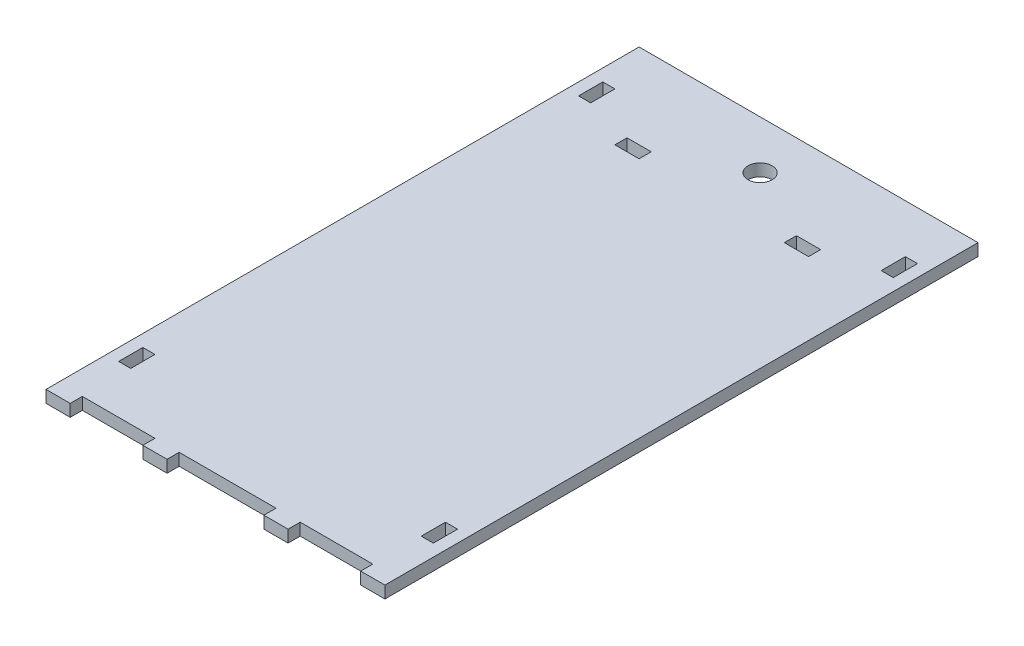
SolidWorks part; units mm, degrees
material "Beech"
ref_plane "Front Plane" through (0, 0, 0) normal (0, 0, 1) x (1, 0, 0)
ref_plane "Top Plane" through (0, 0, 0) normal (0, 1, 0) x (1, 0, 0)
ref_plane "Right Plane" through (0, 0, 0) normal (1, 0, 0) x (0, 0, -1)
sketch "Sketch1" plane through (0, 0, 0) normal (0, 1, 0) x (1, 0, 0)
  line L0 (0, 0) -> (177.8, 0)
  line L1 (0, 0) -> (0, 304.8)
  line L2 (177.8, 0) -> (177.8, 304.8)
  line L3 (0, 304.8) -> (177.8, 304.8)
  line L4 (0, 0) -> (12.7, 0)
  line L5 (0, 0) -> (0, -6.35)
  line L6 (12.7, 0) -> (12.7, -6.35)
  line L7 (0, -6.35) -> (12.7, -6.35)
  line L8 (177.8, 0) -> (165.1, 0)
  line L9 (177.8, 0) -> (177.8, -6.35)
  line L10 (165.1, 0) -> (165.1, -6.35)
  line L11 (177.8, -6.35) -> (165.1, -6.35)
  line L12 (127, 0) -> (114.3, 0)
  line L13 (127, 0) -> (127, -6.35)
  line L14 (114.3, 0) -> (114.3, -6.35)
  line L15 (127, -6.35) -> (114.3, -6.35)
  line L16 (50.8, 0) -> (63.5, 0)
  line L17 (50.8, 0) -> (50.8, -6.35)
  line L18 (63.5, 0) -> (63.5, -6.35)
  line L19 (50.8, -6.35) -> (63.5, -6.35)
  line L20 (165.1, 279.4) -> (171.45, 279.4)
  line L21 (165.1, 279.4) -> (165.1, 266.7)
  line L22 (171.45, 279.4) -> (171.45, 266.7)
  line L23 (165.1, 266.7) -> (171.45, 266.7)
  line L24 (6.35, 279.4) -> (12.7, 279.4)
  line L25 (6.35, 279.4) -> (6.35, 266.7)
  line L26 (12.7, 279.4) -> (12.7, 266.7)
  line L27 (6.35, 266.7) -> (12.7, 266.7)
  line L28 (6.35, 38.1) -> (12.7, 38.1)
  line L29 (6.35, 38.1) -> (6.35, 25.4)
  line L30 (12.7, 38.1) -> (12.7, 25.4)
  line L31 (6.35, 25.4) -> (12.7, 25.4)
  line L32 (165.1, 38.1) -> (171.45, 38.1)
  line L33 (165.1, 38.1) -> (165.1, 25.4)
  line L34 (171.45, 38.1) -> (171.45, 25.4)
  line L35 (165.1, 25.4) -> (171.45, 25.4)
  line L36 (38.1, 260.35) -> (38.1, 254)
  line L37 (38.1, 260.35) -> (50.8, 260.35)
  line L38 (38.1, 254) -> (50.8, 254)
  line L39 (50.8, 260.35) -> (50.8, 254)
  line L40 (127, 260.35) -> (127, 254)
  line L41 (127, 260.35) -> (139.7, 260.35)
  line L42 (127, 254) -> (139.7, 254)
  line L43 (139.7, 260.35) -> (139.7, 254)
  circle A0 centre (88.9, 279.4) radius 6.35
  point P21 (88.9, 304.8)
  dimension "D8" = 12.7
  dimension "D1" = 177.8
  dimension "D2" = 6.35
  dimension "D3" = 12.7
  dimension "D4" = 50.8
  dimension "D5" = 50.8
  dimension "D6" = 304.8
  dimension "D7" = 25.4
  dimension "D9" = 25.4
  dimension "D10" = 25.4
  dimension "D11" = 254
  dimension "D12" = 38.1
  dimension "D13" = 38.1
extrude "Boss-Extrude1" add sketch "Sketch1" along normal blind 6.35 contours L3 L1 L0 L2 A0 L37 L39 L38 L36 L35 L33 L32 L34 L31 L29 L28 L30 L27 L25 L24 L26 L23 L21 L20 L22 L41 L43 L42 L40 | L5 L7 L6 L0 | L17 L19 L18 L0 | L15 L13 L0 L14 | L11 L9 L0 L10
equation "\"CageLeftBottomEdge\"=22.11mm"
equation "\"CageLeftTopEdge\"=22.11mm"
equation "\"CageRightBottomEdge\"=21.63mm"
equation "\"CageRightTopEdge\"=21.63mm"
equation "\"CageHeight\"=86.04mm"
equation "\"CageLength\"=73.76mm"
equation "\"CageTopScrewClearance\"=10mm"
equation "\"CageBottomScrewClearance\"=25mm"
equation "\"CageLeftTopDepth\"= 11.65mm"
equation "\"CageLeftBottomDepth\"=11.11mm"
equation "\"CageLeftTopHeight\"=8.56175mm"
equation "\"CageLeftBottomHeight\"=16mm"
equation "\"CageRightTopDepth\"= 11.05mm"
equation "\"CageRightBottomDepth\"=10.58mm"
equation "\"CageRightTopHeight\"=9.6mm"
equation "\"CageRightBottomHeight\"=15.49mm"
equation "\"CageLeftTopChannelDepth\"=2.41908mm"
equation "\"CageLeftBottomChannelDepth\"=2.588mm"
equation "\"CageLeftChannelHeight\"=11.7mm"
equation "\"CageRightTopChannelDepth\"=2.32mm"
equation "\"CageRightBottomChannelDepth\"=2.318mm"
equation "\"CageRightChannelHeight\"=10mm"
equation "\"CageChanRelHeight\"=23.99mm"
equation "\"CageChanRelDepth\"=5.492mm"
equation "\"CageChamberRadius\"=16.261mm"
equation "\"CageScrewDiameter\"=4.8mm"
equation "\"CageSetScrewDiameter\"=3.5mm"
equation "\"CageAxleRadius\"=6.639mm"
equation "\"CageAxleKeyHeight\"=1.619mm"
equation "\"CageAxleKeyWidth\"=2.662mm"
equation "\"CageHoseWindowWidth\"=16.29mm"
equation "\"CageHoseWindowHeight\"=26.5mm"
equation "\"CageHoseWindow-Edge\"=8.89mm"
equation "\"CageScrew-VerticalEdge\"=5.0mm"
equation "\"CageScrew-HorizontalEdge\"=7.5mm"
equation "\"CageScrew-HoseCornerScrewEdge\"=4.45mm"
equation "\"CageAxle-BottomEdge\"=56.05mm"
equation "\"CageAxle-FrontEdge\"=46.03mm"
equation "\"CageBackSetScrew-Axle\"=40mm"
equation "\"CageFrontSetScrew-Axle\"=22mm"
equation "\"CageVelocityWindow-BackEdge\"=34.8mm"
equation "\"CageVelocityWindow-BottomEdge\"=27.55mm"
equation "\"CageVelocityWindowHeight\"=22.29mm"
equation "\"CageVelocityWindowWidth\"=12.61mm"
equation "\"TriggerSlot-BottomEdge\"=6.35mm"
equation "\"TriggerSlot-FrontEdge\"=15mm"
equation "\"TriggerSlotSize\"=6.7mm"
equation "\"TriggerRackOffset\"=.236224in"
equation "\"TriggerSlotSizeInt\"=.25in"
equation "\"MotorMountLegLength\"=.25in"
equation "\"GearOffset\"=.264907in"
equation "\"TriggerSlotSpacing\"=.25in"
equation "\"TriggerMiniSlotWidth\"=3.5mm"
equation "\"TriggerRackWidth\"=6.5mm"
equation "\"TGMGearFaceDiameter\"=24.40mm"
equation "\"TGMCylinderLength\"=15.00mm"
equation "\"TGMScrewHole-Center\"=8.70mm"
equation "\"TGMScrewHoleDiameter\"=5.04mm"
equation "\"TGMCenterHoleDiameter\"=9.50mm"
equation "\"TGMShaftCollarSideLength\"=19.00mm"
equation "\"TGMShaftCollarDockingDepth\"=7.00mm"
equation "\"whitemotordepth\"=11.27mm"
equation "\"whitemotorbackdepth\"=3.845mm"
equation "\"whitemotoraxledepth\" = 3.5mm"
equation "\"whitemotoraxleoffset\"=11.4mm"
equation "\"whitemotorwidth\"=12.07mm"
equation "\"whitemotorheight\"=16.68mm"
equation "\"whitemotorcylinderlength\" =13.04mm"
equation "\"whitemotorcylinderradius\"=3.845mm"
equation "\"whitemotorcylinderoffset\"=2.35mm"
equation "\"whitemotorcutoutlength\"=1.88mm"
equation "\"whitemotorouterrad\"=5mm"
equation "\"whitemotorinnerrad\"=2.95mm"
equation "\"elasticracklength\"=2in"
equation "\"elasticrackpegsize\"=.25in"
equation "\"elasticrackpegbuffer\"=.125in"
equation "\"elasticrackpegspacing\"=1.76476378in"
equation "\"elasticbaybuffer\"=.25in"
equation "\"elasticdepth\"=.125in"
equation "\"elasticbaydepth\"=.75in"
equation "\"motormountwidth\"=12mm"
equation "\"motormountcornerfillet\"=3mm"
equation "\"pandiscradius\"=14in"
equation "\"towermaterialwidth\"=.25in"
equation "\"towerslotlength\"=.5in"
equation "\"towermarkerspace\"=5in"
equation "\"towerslothorizoffset\"=1in"
equation "\"towerslothorizspacing\"=2in"
equation "\"towerslotvertoffset\"=3in"
equation "\"towerslotvertspacing\"=1in"
equation "\"towerheight\"=12in"
equation "\"towerupslot\"=1in"
equation "\"D1@Sketch1\"=(\"towerslothorizoffset\"+\"towerslothorizspacing\"+\"towerslotlength\")*2"
equation "\"D2@Sketch1\"=\"towermaterialwidth\""
equation "\"D3@Sketch1\"=\"towerslotlength\""
equation "\"D4@Sketch1\"=\"towerslothorizspacing\""
equation "\"D5@Sketch1\"=\"towerslothorizspacing\""
equation "\"D6@Sketch1\"=\"towerheight\""
equation "\"D7@Sketch1\"=\"towerupslot\""
equation "\"toweraxle\"=.5in"
equation "\"D8@Sketch1\"=\"toweraxle\""
equation "\"D9@Sketch1\"=\"towerupslot\""
equation "\"D10@Sketch1\"= \"towerupslot\""
equation "\"D11@Sketch1\" = \"towermotorpanelheight\""
equation "\"towerplatslotoffset\"=1.5in"
equation "\"D12@Sketch1\"=\"towerplatslotoffset\""
equation "\"D13@Sketch1\"=\"towerplatslotoffset\""
equation "\"D1@Boss-Extrude1\"=\"towermaterialwidth\""
equation "\"towermotorpanelheight\"=10in"
equation "\"towerplatdepth\"=2in"
equation "\"stepperouterrad\"=10mm"
equation "\"stepperscrewsize\"=3.45mm"
equation "\"stepperscrewc2c\"=49.5mm"
equation "\"stepperdepthoffset\"=24mm"
equation "\"stepperhorizoffset\"=22.91mm"
equation "\"shaftslotOD\"=18.8mm"
equation "\"shaftslotID\"=13.28mm"
equation "\"shaftkeywidth\"=2.67mm"
equation "\"shaftkeydepth\"=1.8mm"
equation "\"shaftcollartotaldepth\"=12.5mm"
equation "\"shaftsquaredepth\"=6mm"
equation "\"shaftsetscrewsize\"=3.5mm"
equation "\"shaftkeytightdepth\"=1.85mm"
equation "\"shaftslottightID\"=12.78mm"
equation "\"shaftsetscrewoffset\"=9mm"
equation "\"cagecollartotaldepth\"=10mm"
equation "\"cagecollartotalwidth\"=35mm"
equation "\"cagecollarbasedepth\"=4mm"
equation "\"ajaxaxlesize\"=3.87mm"
equation "\"ajaxinnercut\"=2.3mm"
equation "\"ajaxwidth\"=6.1mm"
equation "\"ajaxdiametral\"=25.8854"
equation "\"ajax4020gap\"=29.5mm"
equation "\"ajax4010gap\"=24.5mm"
equation "\"ajaxhubdepth\"=.25in"
equation "\"ajaxcutoutdepth\"=2.3mm"
equation "\"ajax20hubbuffer\"=0.240157in"
equation "\"ajax20hubholeoffset\"=.19685in"
equation "\"ajax20hubholesize\"=.059055in"
equation "\"ajax20cutoutint\"=13.4mm"
equation "\"ajax40hubholesize\"=7.21mm"
equation "\"ajax40hubholeoffset\"=10mm"
equation "\"ajax40hubbuffer\"=.350394in"
equation "\"ajax40cutoutint\"=32.6mm"
equation "\"no6diam\"=.146in"
equation "\"shconangle\"=20deg"
equation "\"shconlen\"=1in"
equation "\"lnconlen\"=1.5in"
equation "\"lnconangle\"=15deg"
